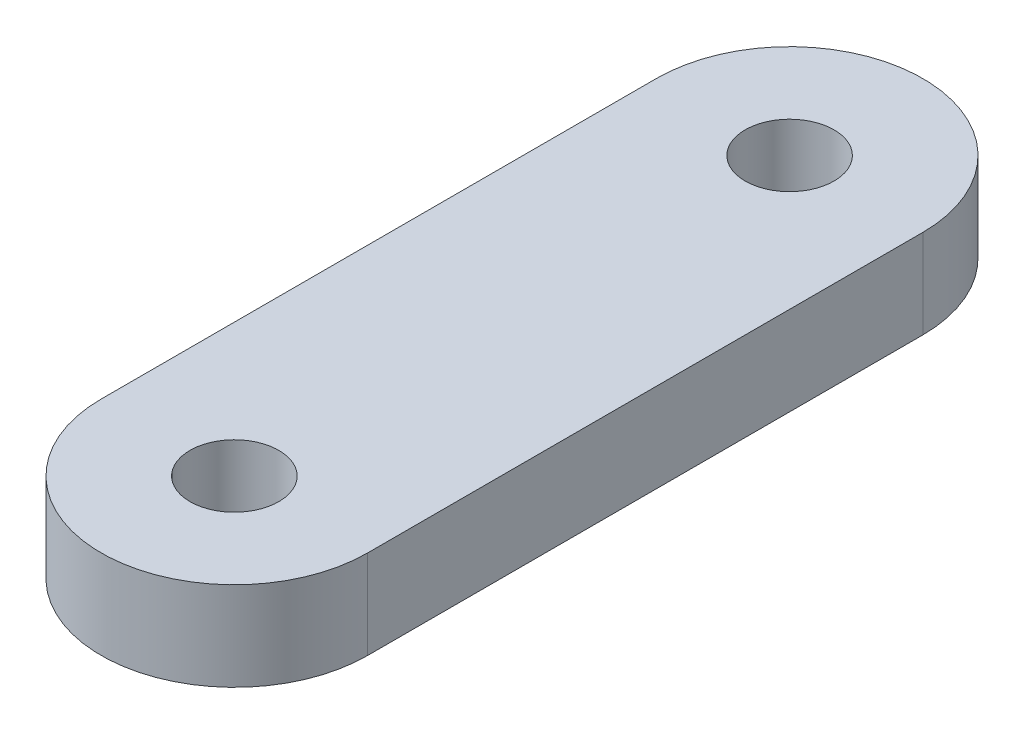
SolidWorks part; units mm, degrees
ref_plane "Front Plane" through (0, 0, 0) normal (0, 0, 1) x (1, 0, 0)
ref_plane "Top Plane" through (0, 0, 0) normal (0, 1, 0) x (1, 0, 0)
ref_plane "Right Plane" through (0, 0, 0) normal (1, 0, 0) x (0, 0, -1)
sketch "Sketch1" plane through (0, 0, 0) normal (0, 1, 0) x (1, 0, 0)
  line L0 (0, 12.5) -> (0, -12.5) construction
  line L1 (6, 12.5) -> (6, -12.5)
  line L2 (-6, 12.5) -> (-6, -12.5)
  arc A0 (6, 12.5) -> (-6, 12.5) centre (0, 12.5) ccw
  arc A1 (-6, -12.5) -> (6, -12.5) centre (0, -12.5) ccw
  point P2 (0, 0)
  dimension "D2" = 6
  dimension "D1" = 25
extrude "Boss-Extrude1" add sketch "Sketch1" along normal blind 4
sketch "Sketch2" plane through (0, 4, 0) normal (0, 1, 0) x (1, 0, 0)
  circle A0 centre (0, 12.5) radius 2
  circle A1 centre (0, -12.5) radius 2
  dimension "D1" = 4
  dimension "D2" = 4
extrude "Cut-Extrude3" cut sketch "Sketch2" against normal through all
